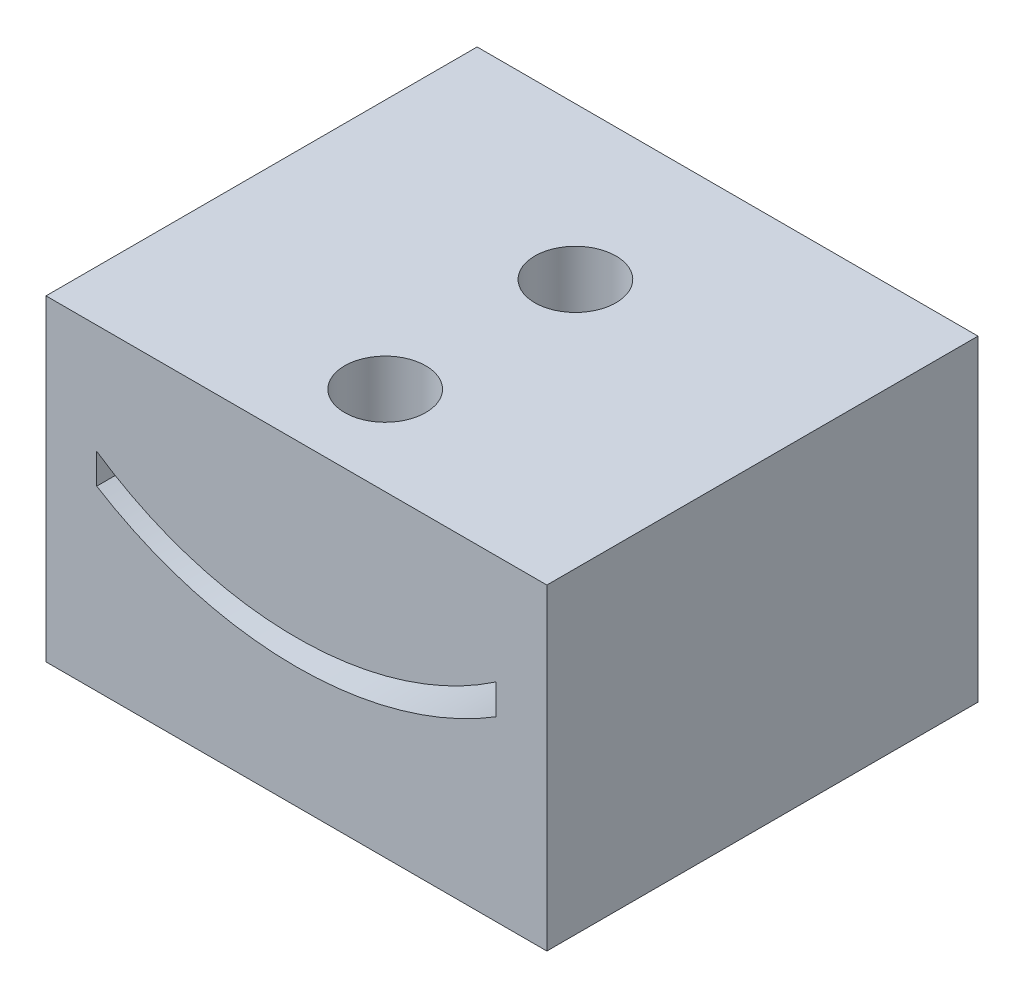
SolidWorks part; units mm, degrees
ref_plane "Front plane" through (0, 0, 0) normal (0, 0, 1) x (1, 0, 0)
ref_plane "Top plane" through (0, 0, 0) normal (0, 1, 0) x (1, 0, 0)
ref_plane "Right Plane" through (0, 0, 0) normal (1, 0, 0) x (0, 0, -1)
sketch "Sketch1" plane through (0, 0, 0) normal (0, 0, 1) x (1, 0, 0)
  line L0 (0, 0) -> (19.75, 0)
  line L1 (19.75, 0) -> (19.75, 12.5)
  line L2 (19.75, 12.5) -> (0, 12.5)
  line L4 (17.75, 8.1914) -> (17.75, 7)
  line L8 (2, 8.1914) -> (2, 7)
  line L10 (0, 12.5) -> (0, 0)
  arc A0 (2, 8.1914) -> (17.75, 8.1914) centre (9.875, 19.7665) ccw
  arc A1 (2, 7) -> (17.75, 7) centre (9.875, 19.7665) ccw
  dimension "D1" = 15
  dimension "D2" = 1
  dimension "D3" = 2
  dimension "D4" = 15.75
  dimension "D5" = 7
  dimension "D6" = 12.5
  dimension "D7" = 2
extrude "Boss-Extrude1" add sketch "Sketch1" along normal blind 15
sketch "Sketch2" plane through (0, 12.5, 0) normal (0, 1, 0) x (1, 0, 0)
  line L0 (2, 0) -> (17.75, -15) construction
  line L1 (19.75, -15) -> (0, -15) construction
  line L2 (19.75, 0) -> (0, 0) construction
  line L3 (19.75, 0) -> (0, 0) construction
  circle A0 centre (9.875, -11.5) radius 1.6
  circle A1 centre (9.875, -4) radius 1.6
  point P12 (9.875, -7.5)
  dimension "D1" = 3.2
  dimension "D2" = 7.5
  dimension "D3" = 4
extrude "Cut-Extrude1" cut sketch "Sketch2" against normal through all
sketch "Sketch3" plane through (0, 0, 0) normal (0, 0, -1) x (-1, 0, 0)
  line L1 (0, 12.5) -> (-19.75, 12.5)
  line L2 (0, 12.5) -> (0, 0)
  line L3 (0, 0) -> (-19.75, 0)
  line L4 (-19.75, 12.5) -> (-19.75, 0)
extrude "Boss-Extrude2" add sketch "Sketch3" along normal blind 2
